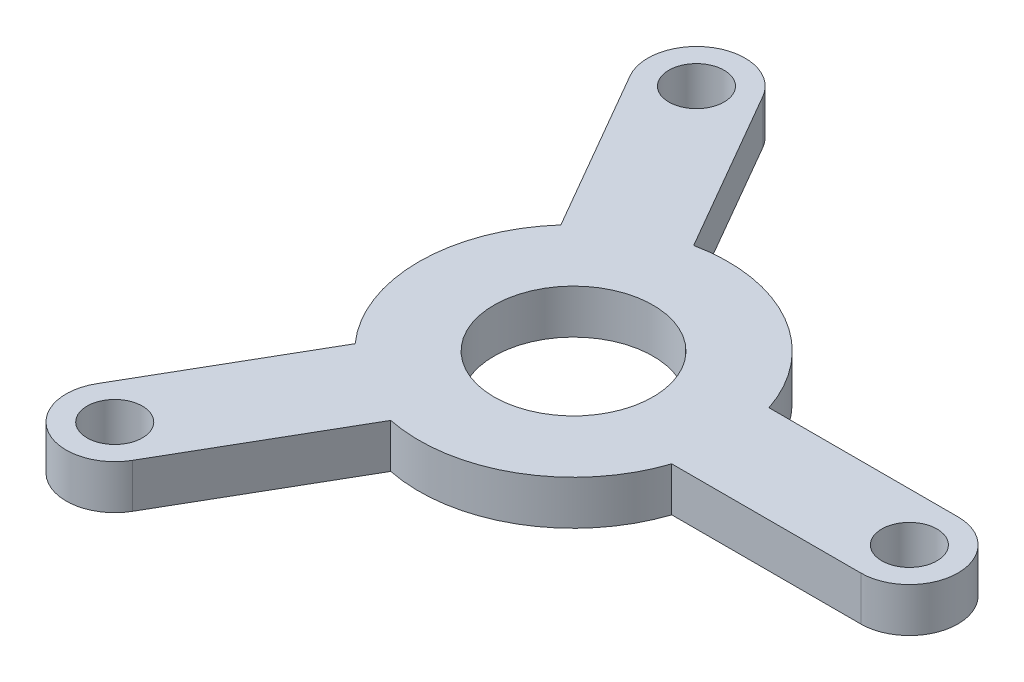
SolidWorks part; units mm, degrees
ref_plane "Front Plane" through (0, 0, 0) normal (0, 0, 1) x (1, 0, 0)
ref_plane "Top Plane" through (0, 0, 0) normal (0, 1, 0) x (1, 0, 0)
ref_plane "Right Plane" through (0, 0, 0) normal (1, 0, 0) x (0, 0, -1)
sketch "Sketch1" plane through (0, 0, 0) normal (0, 1, 0) x (1, 0, 0)
  circle A0 centre (0, 0) radius 9
  circle A1 centre (0, 0) radius 17.5
  dimension "D1" = 18
  dimension "D2" = 35
extrude "Boss-Extrude1" add sketch "Sketch1" along normal blind 5
sketch "Sketch3" plane through (0, 0, 0) normal (0, 1, 0) x (1, 0, 0)
  line L0 (0, 0) -> (38, 0) construction
  line L1 (10.0099, 5.5) -> (38, 5.5)
  line L2 (10.0099, 5.5) -> (10.0099, -5.5)
  line L3 (38, 5.5) -> (38, -5.5)
  line L4 (10.0099, -5.5) -> (38, -5.5)
  line L5 (38, 0) -> (10.0099, 0) construction
  line L6 (24.005, 5.5) -> (24.005, -5.5) construction
  circle A0 centre (0, 0) radius 38 construction
  circle A1 centre (38, 0) radius 5.5
  point P6 (24.005, 0)
  dimension "D1" = 76
  dimension "D2" = 11
  dimension "D3" = 11
extrude "Boss-Extrude3" add sketch "Sketch3" along normal up to surface (5 mm away) contours A1 L1 L2 L4 | L3 A1 | L3 A1 up to face at (0, 5, 17.5)
sketch "Sketch4" plane through (0, 5, 0) normal (0, 1, 0) x (1, 0, 0)
  circle A0 centre (38, 0) radius 3.125
  dimension "D1" = 6.25
extrude "Cut-Extrude1" cut sketch "Sketch4" against normal through all both and the other way through all
pattern_circular "CirPattern1" count 3 over 360 about axis through (0, 0, 0) along (0, 1, 0) of "Boss-Extrude3", "Cut-Extrude1"
